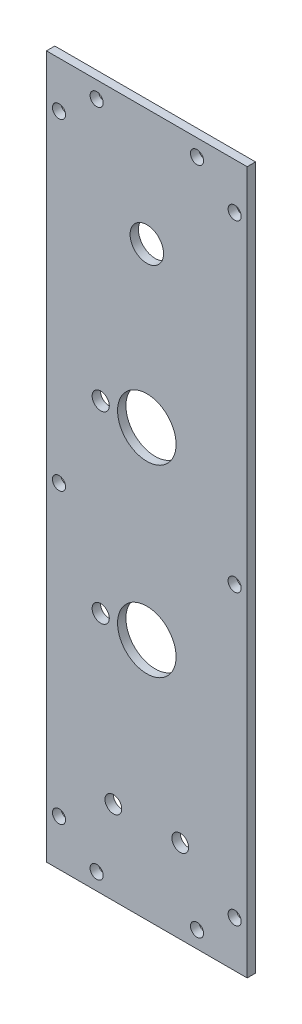
SolidWorks part; units mm, degrees
ref_plane "Front Plane" through (0, 0, 0) normal (0, 0, 1) x (1, 0, 0)
ref_plane "Top Plane" through (0, 0, 0) normal (0, 1, 0) x (1, 0, 0)
ref_plane "Right Plane" through (0, 0, 0) normal (1, 0, 0) x (0, 0, -1)
sketch "Sketch1" plane through (0, 0, 0) normal (0, 0, 1) x (1, 0, 0)
  line L0 (57.15, -6.35) -> (57.15, -260.35) construction
  line L1 (0, 0) -> (76.2, 0)
  line L2 (0, 0) -> (0, -266.7)
  line L3 (0, -266.7) -> (76.2, -266.7)
  line L4 (76.2, 0) -> (76.2, -266.7)
  line L5 (19.05, -6.35) -> (19.05, -260.35) construction
  line L6 (4.7625, -17.4625) -> (4.7625, -249.2375) construction
  line L7 (71.4375, -17.4625) -> (71.4375, -249.2375) construction
  circle A0 centre (19.05, -6.35) radius 2.4892
  circle A1 centre (57.15, -6.35) radius 2.4892
  circle A2 centre (71.4375, -17.4625) radius 2.4892
  circle A3 centre (4.7625, -17.4625) radius 2.4892
  circle A4 centre (71.4375, -139.7) radius 2.4892
  circle A5 centre (4.7625, -139.7) radius 2.4892
  circle A6 centre (71.4375, -249.2375) radius 2.4892
  circle A7 centre (4.7625, -249.2375) radius 2.4892
  circle A8 centre (19.05, -260.35) radius 2.4892
  circle A9 centre (57.15, -260.35) radius 2.4892
  dimension "D12" = 4.9784
  dimension "D1" = 76.2
  dimension "D2" = 266.7
  dimension "D3" = 19.05
  dimension "D4" = 19.05
  dimension "D5" = 6.35
  dimension "D6" = 6.35
  dimension "D7" = 4.7625
  dimension "D8" = 4.7625
  dimension "D9" = 17.4625
  dimension "D10" = 17.4625
  dimension "D11" = 127
extrude "Boss-Extrude1" add sketch "Sketch1" along normal blind 3.175
sketch "Sketch2" plane through (0, 0, 3.175) normal (0, 0, 1) x (1, 0, 0)
  line L2 (0, -266.7) -> (76.2, -266.7) construction
  line L4 (76.2, -266.7) -> (76.2, 0) construction
  line L5 (0, 0) -> (0, -266.7) construction
  line L6 (76.2, 0) -> (0, 0) construction
  circle A0 centre (38.1, -104.775) radius 11.1125
  circle A1 centre (38.1, -174.625) radius 11.1125
  circle A2 centre (20.5999, -174.625) radius 3.2512
  circle A3 centre (20.5999, -104.775) radius 3.2512
  circle A4 centre (25.4, -234.95) radius 3.175
  circle A5 centre (50.8, -234.95) radius 3.175
  circle A6 centre (38.1, -44.45) radius 6.35
  dimension "D4" = 22.225
  dimension "D5" = 17.5001
  dimension "D6" = 6.5024
  dimension "D7" = 31.75
  dimension "D10" = 6.35
  dimension "D11" = 44.45
  dimension "D12" = 12.7
  dimension "D1" = 92.075
  dimension "D2" = 38.1
  dimension "D3" = 69.85
  dimension "D8" = 25.4
  dimension "D9" = 25.4
  dimension "D13" = 38.1
extrude "Cut-Extrude1" cut sketch "Sketch2" against normal blind 3.175
